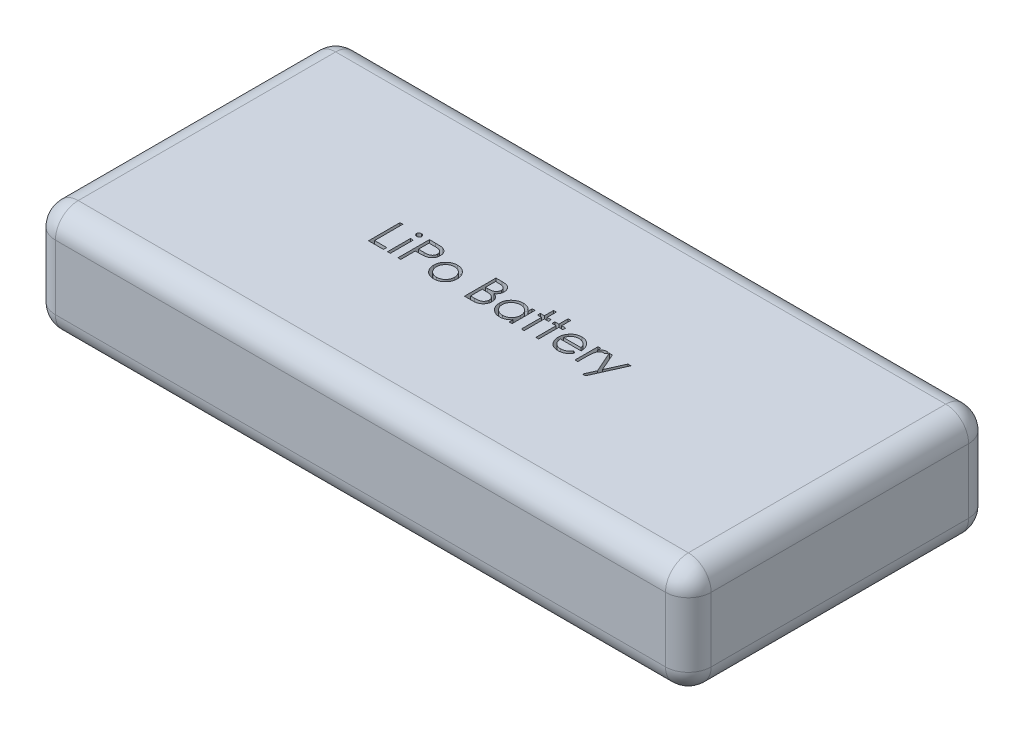
SolidWorks part; units mm, degrees
ref_plane "Front Plane" through (0, 0, 0) normal (0, 0, 1) x (1, 0, 0)
ref_plane "Top Plane" through (0, 0, 0) normal (0, 1, 0) x (1, 0, 0)
ref_plane "Right Plane" through (0, 0, 0) normal (1, 0, 0) x (0, 0, -1)
sketch "Sketch1" plane through (0, 0, 0) normal (0, 1, 0) x (1, 0, 0)
  line L1 (0, 0) -> (72.9742, 0)
  line L2 (0, 0) -> (0, 33.7312)
  line L3 (0, 33.7312) -> (72.9742, 33.7312)
  line L4 (72.9742, 0) -> (72.9742, 33.7312)
  dimension "D1" = 72.9742
  dimension "D2" = 33.7312
extrude "Boss-Extrude1" add sketch "Sketch1" along normal blind 12.2682
sketch "Sketch2" plane through (0, 12.2682, 0) normal (0, 1, 0) x (1, 0, 0)
  text T0 "LiPo Battery"
extrude "Cut-Extrude1" cut sketch "Sketch2" against normal blind 1.778
fillet "Fillet1" radius 2.54 12 edges at (0, 12.2682, -16.8656) (0, 0, -16.8656) (0, 6.1341, 0) (36.4871, 12.2682, 0) (36.4871, 0, 0) (72.9742, 6.1341, 0) (72.9742, 12.2682, -16.8656) (72.9742, 0, -16.8656) (72.9742, 6.1341, -33.7312) (36.4871, 12.2682, -33.7312) (0, 6.1341, -33.7312) (36.4871, 0, -33.7312)
